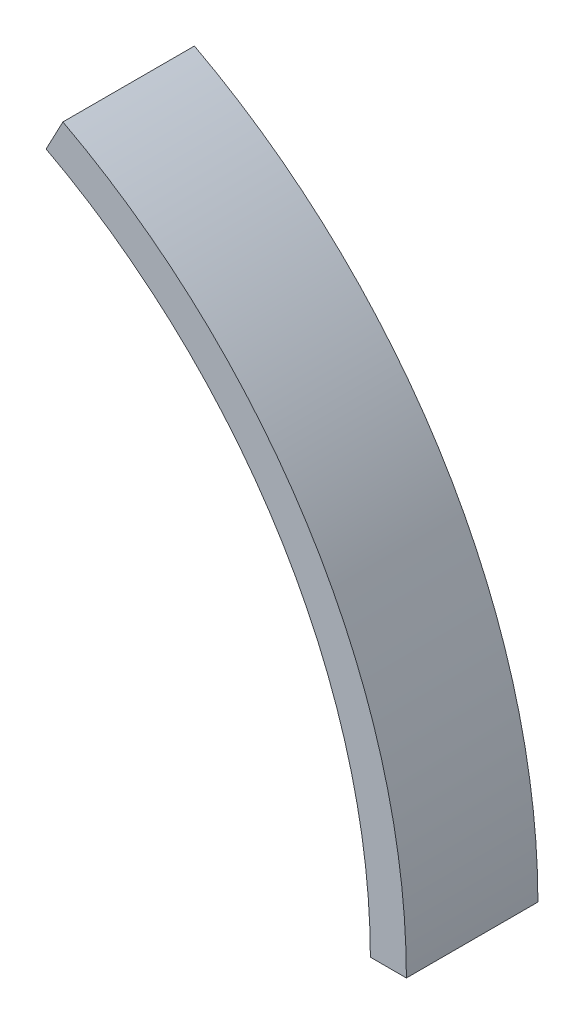
SolidWorks part; units mm, degrees
ref_plane "Front Plane" through (0, 0, 0) normal (0, 0, 1) x (1, 0, 0)
ref_plane "Top Plane" through (0, 0, 0) normal (0, 1, 0) x (1, 0, 0)
ref_plane "Right Plane" through (0, 0, 0) normal (1, 0, 0) x (0, 0, -1)
sketch "Sketch1" plane through (0, 0, 0) normal (0, 0, 1) x (1, 0, 0)
  line L0 (-20.0025, 37.909) -> (-20.0025, 78.5792) construction
  line L1 (20.0025, 37.909) -> (20.0025, 78.5792) construction
  line L2 (0, 0) -> (42.8625, 0) construction
  line L3 (20.0025, 37.909) -> (21.1878, 40.1555)
  line L4 (42.8625, 0) -> (45.4025, 0)
  arc A0 (42.8625, 0) -> (-20.0025, 37.909) centre (0, 0) ccw construction
  arc A1 (42.8625, 0) -> (20.0025, 37.909) centre (0, 0) ccw
  arc A2 (45.4025, 0) -> (21.1878, 40.1555) centre (0, 0) ccw
  dimension "D1" = 85.725
  dimension "D2" = 40.005
  dimension "D3" = 2.54
extrude "Boss-Extrude1" add sketch "Sketch1" along normal mid plane 9.271
